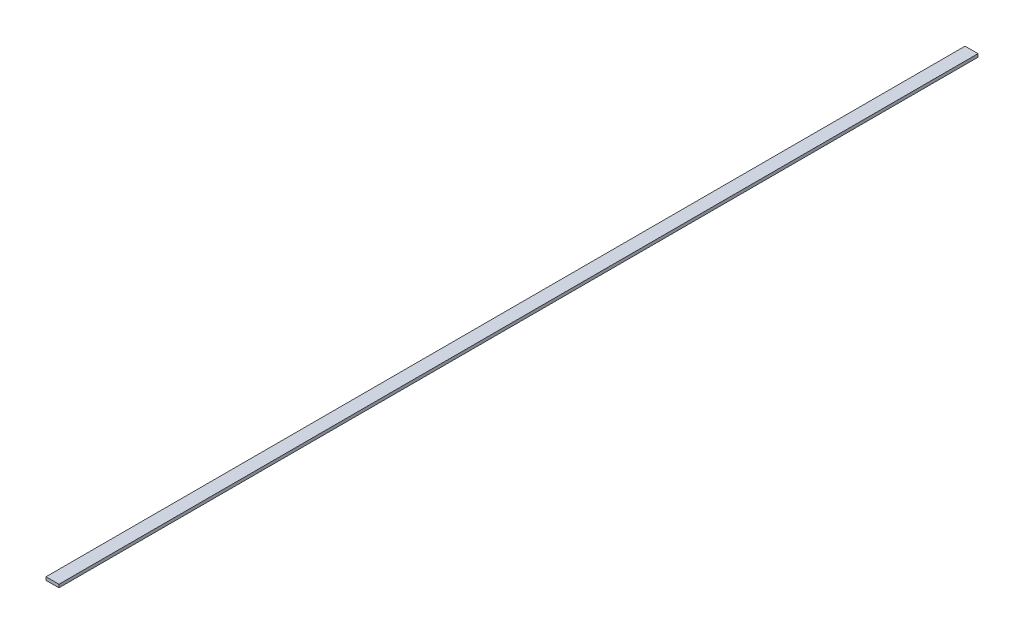
SolidWorks part; units mm, degrees
ref_plane "Alzado" through (0, 0, 0) normal (0, 0, 1) x (1, 0, 0)
ref_plane "Planta" through (0, 0, 0) normal (0, 1, 0) x (1, 0, 0)
ref_plane "Vista lateral" through (0, 0, 0) normal (1, 0, 0) x (0, 0, -1)
sketch "Croquis1" plane through (0, 0, 0) normal (0, 1, 0) x (1, 0, 0)
  line L1 (0, 0) -> (6.2, 0)
  line L2 (0, 0) -> (0, 440)
  line L3 (0, 440) -> (6.2, 440)
  line L4 (6.2, 0) -> (6.2, 440)
  dimension "D1" = 440
  dimension "D2" = 6.2
extrude "Saliente-Extruir1" add sketch "Croquis1" along normal blind 1.5
